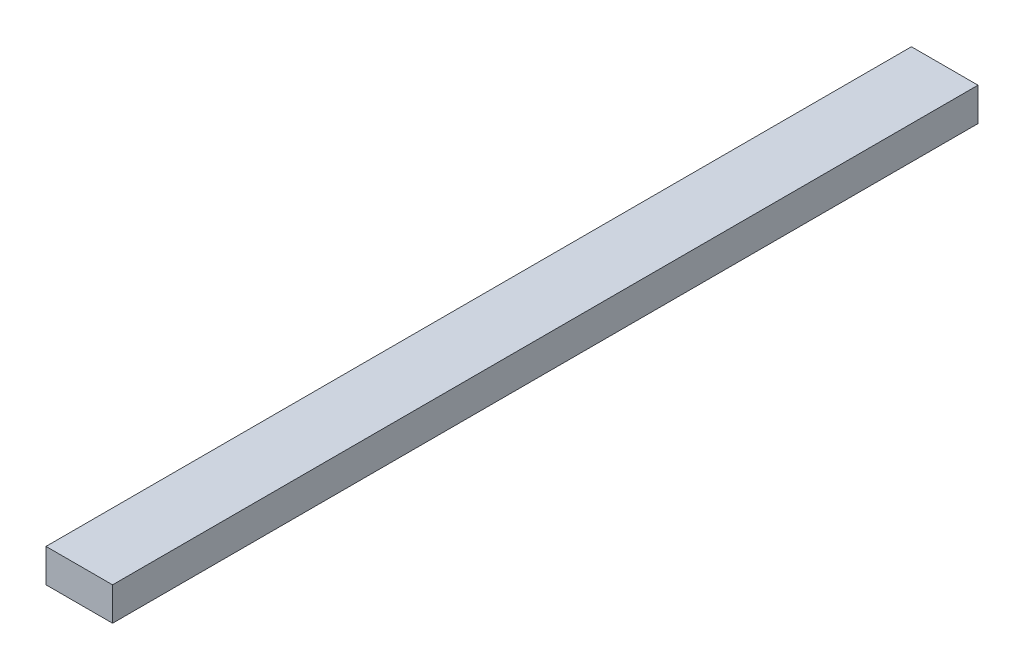
SolidWorks part; units mm, degrees
ref_plane "Front Plane" through (0, 0, 0) normal (0, 0, 1) x (1, 0, 0)
ref_plane "Top Plane" through (0, 0, 0) normal (0, 1, 0) x (1, 0, 0)
ref_plane "Right Plane" through (0, 0, 0) normal (1, 0, 0) x (0, 0, -1)
sketch "Sketch2" plane through (0, 0, 0) normal (0, 0, 1) x (1, 0, 0)
  line L1 (0, 0) -> (50.8, 0)
  line L2 (0, 0) -> (0, 25.4)
  line L3 (0, 25.4) -> (50.8, 25.4)
  line L4 (50.8, 0) -> (50.8, 25.4)
  dimension "D1" = 50.8
  dimension "D2" = 25.4
extrude "Boss-Extrude1" add sketch "Sketch2" along normal blind 660.4
